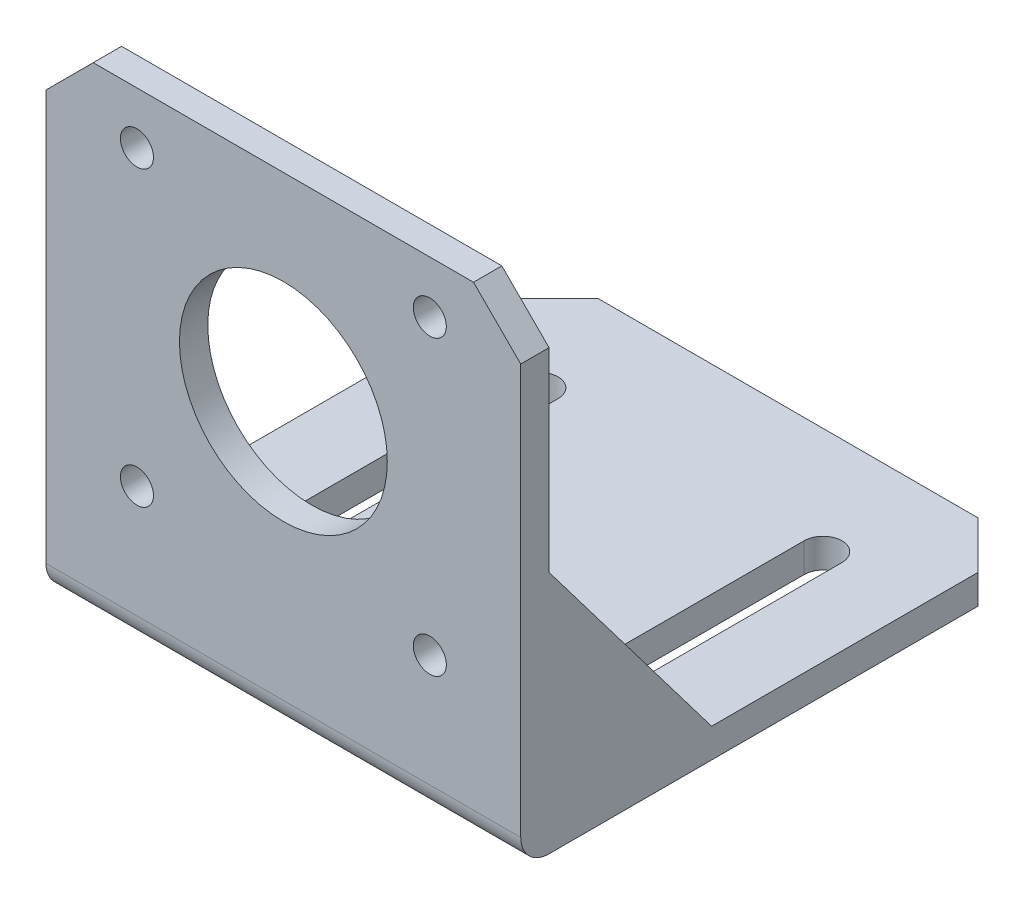
SolidWorks part; units mm, degrees
ref_plane "Front" through (0, 0, 0) normal (0, 0, 1) x (1, 0, 0)
ref_plane "Top" through (0, 0, 0) normal (0, 1, 0) x (1, 0, 0)
ref_plane "Right" through (0, 0, 0) normal (1, 0, 0) x (0, 0, -1)
sketch "Sketch1" plane through (0, 0, 0) normal (0, 0, 1) x (1, 0, 0)
  line L0 (0, 46.4) -> (5, 51.4)
  line L1 (0, 0) -> (50.25, 0)
  line L2 (0, 0) -> (0, 46.4)
  line L3 (5, 51.4) -> (45.25, 51.4)
  line L4 (50.25, 0) -> (50.25, 46.4)
  line L5 (25.125, 0) -> (25.125, 51.4) construction
  line L6 (50.25, 46.4) -> (45.25, 51.4)
  line L7 (0, 30.4) -> (50.25, 30.4) construction
  circle A0 centre (25.125, 30.4) radius 11
  circle A1 centre (9.625, 45.9) radius 1.75
  circle A2 centre (40.625, 45.9) radius 1.75
  circle A3 centre (40.625, 14.9) radius 1.75
  circle A4 centre (9.625, 14.9) radius 1.75
  dimension "D5" = 22
  dimension "D6" = 10
  dimension "D7" = 3.5
  dimension "D8" = 31
  dimension "D9" = 31
  dimension "D1" = 5
  dimension "D2" = 5
  dimension "D3" = 51.4
  dimension "D4" = 50.25
extrude "Boss-Extrude1" add sketch "Sketch1" along normal blind 3
sketch "Sketch2" plane through (0, 0, 0) normal (0, -1, 0) x (1, 0, 0)
  line L0 (0, 3) -> (50.25, 3) construction
  line L1 (0, 3) -> (50.25, 3)
  line L2 (0, 3) -> (0, -45.4)
  line L3 (5, -50.4) -> (45.25, -50.4)
  line L4 (50.25, 3) -> (50.25, -45.4)
  line L5 (50.25, -45.4) -> (45.25, -50.4)
  line L6 (25.125, 3) -> (25.125, -50.4) construction
  line L7 (0, -45.4) -> (5, -50.4)
  line L8 (40.15, -9.1) -> (40.15, -39.1) construction
  line L9 (42.15, -9.1) -> (42.15, -39.1)
  line L10 (38.15, -9.1) -> (38.15, -39.1)
  line L11 (10.1, -9.1) -> (10.1, -39.1) construction
  line L12 (8.1, -9.1) -> (8.1, -39.1)
  line L13 (12.1, -9.1) -> (12.1, -39.1)
  arc A0 (42.15, -9.1) -> (38.15, -9.1) centre (40.15, -9.1) ccw
  arc A1 (38.15, -39.1) -> (42.15, -39.1) centre (40.15, -39.1) ccw
  arc A2 (8.1, -9.1) -> (12.1, -9.1) centre (10.1, -9.1) cw
  arc A3 (12.1, -39.1) -> (8.1, -39.1) centre (10.1, -39.1) cw
  point P13 (40.15, -24.1)
  point P20 (10.1, -24.1)
  dimension "D5" = 9.3
  dimension "D6" = 34
  dimension "D1" = 5
  dimension "D2" = 5
  dimension "D3" = 53.4
  dimension "D4" = 4
  dimension "D7" = 8.1
extrude "Boss-Extrude2" add sketch "Sketch2" against normal blind 3.1
sketch "Sketch3" plane through (0, 0, 0) normal (-1, 0, 0) x (0, 0, 1)
  line L0 (0, 25.8) -> (-17.2, 3.1)
  line L1 (3, 0) -> (-17.2, 0)
  line L2 (3, 0) -> (3, 25.8)
  line L3 (3, 25.8) -> (0, 25.8)
  line L4 (-17.2, 0) -> (-17.2, 3.1)
  line L5 (0, 3.1) -> (-45.4, 3.1) construction
  line L6 (0, 46.4) -> (0, 3.1) construction
  dimension "D1" = 17.2
  dimension "D2" = 22.7
extrude "Boss-Extrude3" add sketch "Sketch3" against normal blind 2.6
ref_plane "Plane1" through (25.125, 0, 0) normal (-1, 0, 0) x (0, 0, 1)
mirror "Mirror1" about plane through (25.125, 0, 0) normal (-1, 0, 0) of "Boss-Extrude3"
fillet "Fillet1" radius 3 1 edges at (25.125, 0, 3)
fillet "Fillet2" radius 3 1 edges at (25.125, 3.1, 0)
